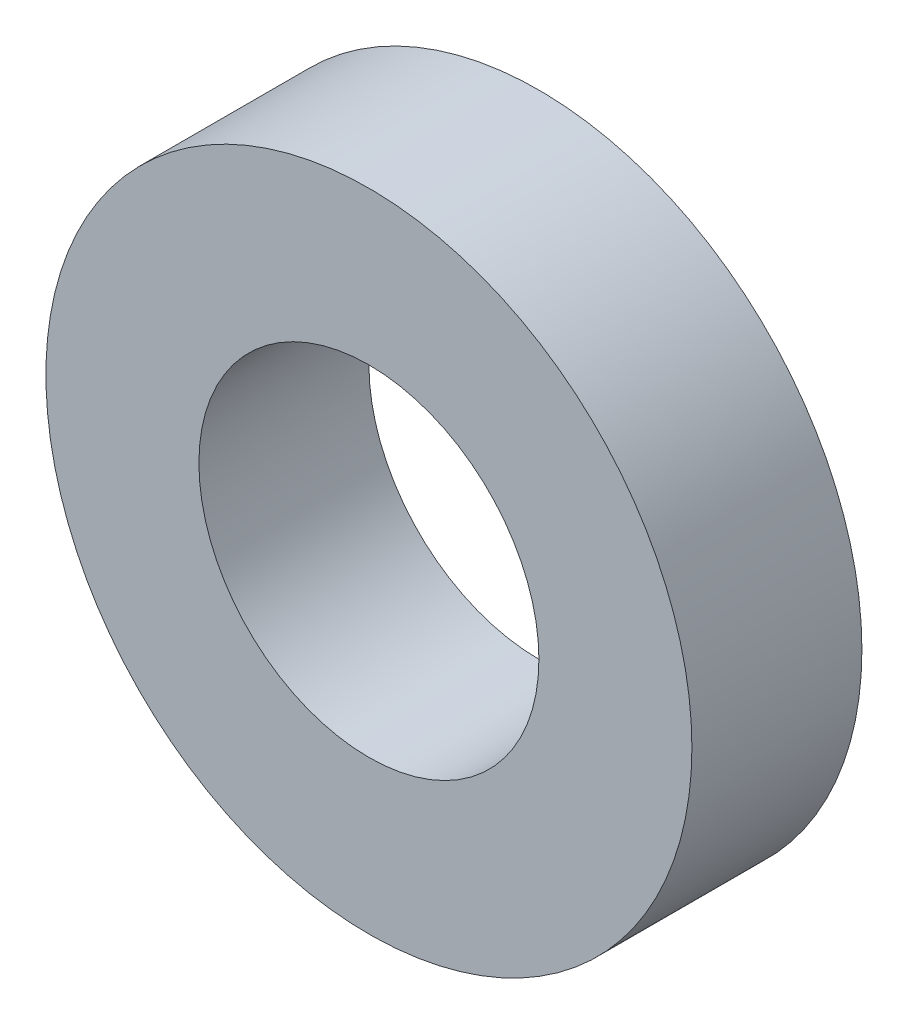
SolidWorks part; units mm, degrees
material "Comercialmente puro CP-Ti UNS R50400 (SS)"
ref_plane "Alzado" through (0, 0, 0) normal (0, 0, 1) x (1, 0, 0)
ref_plane "Planta" through (0, 0, 0) normal (0, 1, 0) x (1, 0, 0)
ref_plane "Vista lateral" through (0, 0, 0) normal (1, 0, 0) x (0, 0, -1)
sketch "Croquis1" plane through (0, 0, 0) normal (0, 0, 1) x (1, 0, 0)
  circle A0 centre (0, 0) radius 9.5
  dimension "D1" = 19
extrude "Saliente-Extruir1" add sketch "Croquis1" along normal blind 5
sketch "Croquis2" plane through (0, 0, 5) normal (0, 0, 1) x (1, 0, 0)
  circle A0 centre (0, 0) radius 5
  dimension "D1" = 10
extrude "Cortar-Extruir1" cut sketch "Croquis2" against normal blind 6.35 contours A0
